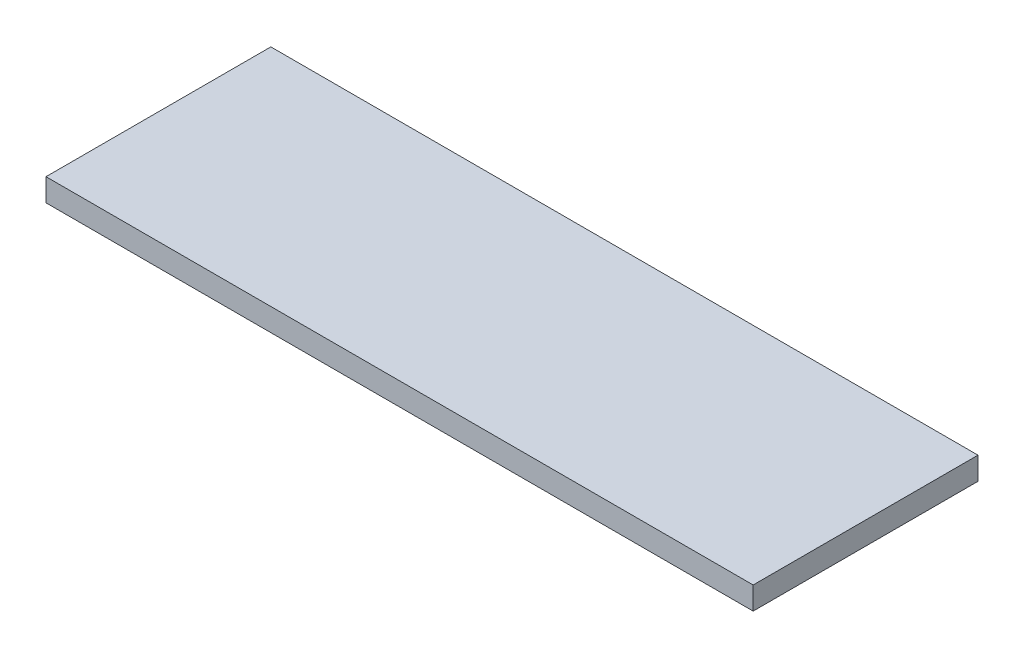
SolidWorks part; units mm, degrees
material "AISI 1020"
ref_plane "Front Plane" through (0, 0, 0) normal (0, 0, 1) x (1, 0, 0)
ref_plane "Top Plane" through (0, 0, 0) normal (0, 1, 0) x (1, 0, 0)
ref_plane "Right Plane" through (0, 0, 0) normal (1, 0, 0) x (0, 0, -1)
sketch "Sketch1" plane through (0, 0, 0) normal (0, 1, 0) x (1, 0, 0)
  line L1 (-99.06, -31.496) -> (99.06, -31.496)
  line L2 (-99.06, -31.496) -> (-99.06, 31.496)
  line L3 (-99.06, 31.496) -> (99.06, 31.496)
  line L4 (99.06, -31.496) -> (99.06, 31.496)
  line L5 (-99.06, -31.496) -> (99.06, 31.496) construction
  line L6 (-99.06, 31.496) -> (99.06, -31.496) construction
  point P0 (0, 0)
  dimension "D1" = 198.12
  dimension "D2" = 62.992
extrude "Boss-Extrude1" add sketch "Sketch1" along normal blind 6.35
